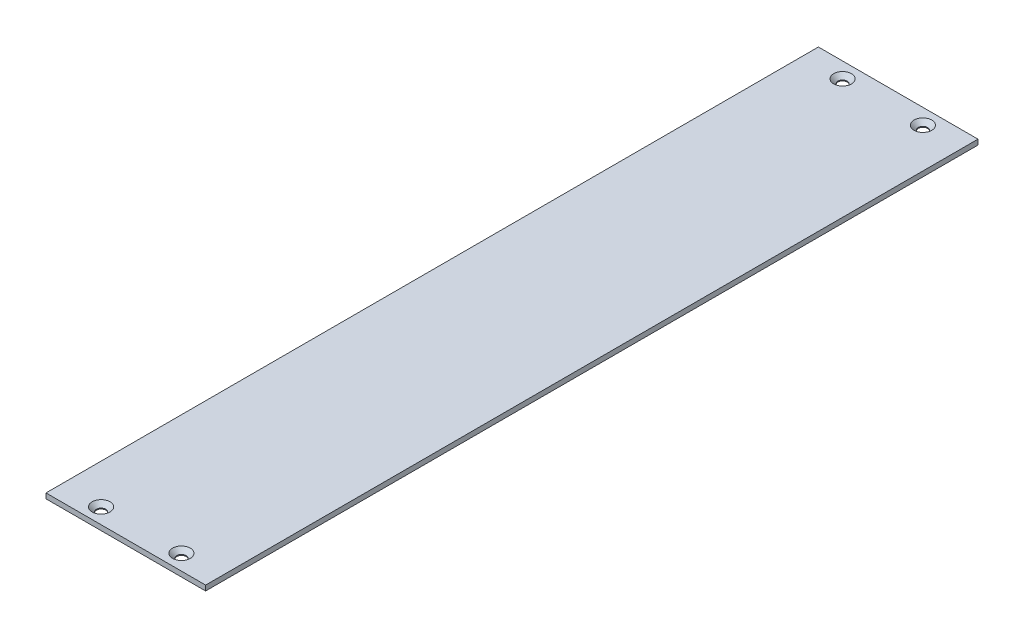
SolidWorks part; units mm, degrees
material "Acrylic (Medium-high impact)"
ref_plane "Front Plane" through (0, 0, 0) normal (0, 0, 1) x (1, 0, 0)
ref_plane "Top Plane" through (0, 0, 0) normal (0, 1, 0) x (1, 0, 0)
ref_plane "Right Plane" through (0, 0, 0) normal (1, 0, 0) x (0, 0, -1)
sketch "Sketch1" plane through (0, 0, 0) normal (0, 1, 0) x (1, 0, 0)
  line L1 (0, 0) -> (155, 0)
  line L2 (0, 0) -> (0, -750)
  line L3 (0, -750) -> (155, -750)
  line L4 (155, 0) -> (155, -750)
  line L5 (0, 0) -> (155, -750) construction
  line L6 (0, -750) -> (155, 0) construction
  point P4 (77.5, -375)
  dimension "D1" = 155
  dimension "D2" = 750
extrude "Boss-Extrude1" add sketch "Sketch1" along normal blind 5
sketch "Sketch2" plane through (0, 5, 0) normal (0, 1, 0) x (1, 0, 0)
  line L1 (155, 0) -> (106.5, 0)
  line L2 (155, 0) -> (155, -30)
  line L3 (155, -30) -> (106.5, -30)
  line L4 (106.5, 0) -> (106.5, -30)
  line L5 (155, 0) -> (106.5, -30) construction
  line L6 (155, -30) -> (106.5, 0) construction
  point P4 (130.75, -15)
  dimension "D1" = 30
  dimension "D2" = 48.5
hole_wizard "CSK for M8 Flat Head Machine Screw1" positions "Sketch23" profile "Sketch24" countersink size "M8" standard "ANSI Metric" end condition through all
sketch "Sketch23" plane through (0, 5, 0) normal (0, 1, 0) x (1, 0, 0)
  line L0 (106.5, 0) -> (106.5, -30) construction
  point P0 (116.5, -15)
  dimension "D1" = 10
sketch "Sketch24" plane through (116.5, 5, 15) normal (1, 0, 0) x (0, 0, 1)
  line L0 (0, 0) -> (0, 5)
  line L1 (0, 5) -> (4.5, 5)
  line L2 (4.5, 5) -> (4.5, 4.15)
  line L3 (4.5, 4.15) -> (8.65, 0)
  line L5 (8.65, 0) -> (0, 0)
  line L6 (-4.5, 4.15) -> (-8.65, 0) construction
  line L11 (0, -6.35) -> (0, 107.95) construction
  dimension "Thru Hole Dia." = 9
  dimension "Thru Hole Depth" = 5
  dimension "Near C'Sink Dia." = 17.3
  dimension "Near C'Sink Angle" = 90
ref_plane "Plane1" through (77.5, 0, 0) normal (1, 0, 0) x (0, 0, -1)
ref_plane "Plane2" through (0, 0, 375) normal (0, 0, -1) x (-1, 0, 0)
mirror "Mirror1" about plane through (0, 0, 375) normal (0, 0, -1) of "CSK for M8 Flat Head Machine Screw1"
mirror "Mirror2" about plane through (77.5, 0, 0) normal (1, 0, 0) of "Mirror1", "CSK for M8 Flat Head Machine Screw1"
